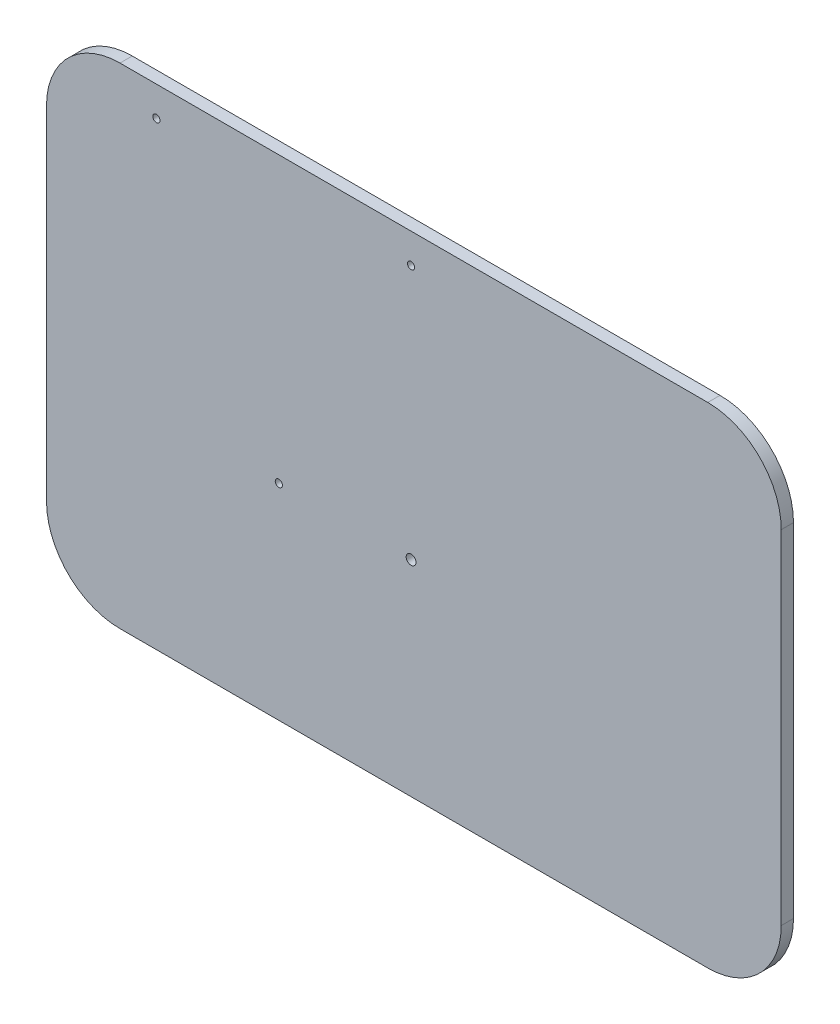
SolidWorks part; units mm, degrees
ref_plane "Alzado" through (0, 0, 0) normal (0, 0, 1) x (1, 0, 0)
ref_plane "Planta" through (0, 0, 0) normal (0, 1, 0) x (1, 0, 0)
ref_plane "Vista lateral" through (0, 0, 0) normal (1, 0, 0) x (0, 0, -1)
sketch "Croquis1" plane through (0, 0, 0) normal (0, 0, 1) x (1, 0, 0)
  line L1 (30, 0) -> (270, 0)
  line L2 (0, 30) -> (0, 170)
  line L3 (30, 200) -> (270, 200)
  line L4 (300, 30) -> (300, 170)
  arc A0 (30, 0) -> (0, 30) centre (30, 30) cw
  arc A1 (270, 0) -> (300, 30) centre (270, 30) ccw
  arc A2 (270, 200) -> (300, 170) centre (270, 170) cw
  arc A3 (0, 170) -> (30, 200) centre (30, 170) cw
  point P7 (0, 0)
  point P12 (300, 200)
  point P15 (0, 200)
  dimension "D3" = 30
  dimension "D1" = 200
  dimension "D2" = 300
extrude "Saliente-Extruir1" add sketch "Croquis1" along normal blind 5
sketch "Croquis2" plane through (0, 0, 0) normal (0, 0, -1) x (-1, 0, 0)
  line L0 (0, 170) -> (0, 30) construction
  line L1 (-270, 200) -> (-30, 200) construction
  circle A0 centre (-148.8517, 187.8414) radius 1.4655
  circle A1 centre (-44.8517, 187.8414) radius 1.4655
  circle A2 centre (-94.8517, 83.8414) radius 1.4655
  circle A3 centre (-148.8517, 83.8414) radius 2
  point P12 (-44.8517, 187.8414)
  dimension "D1" = 4
  dimension "D2" = 44.8517
  dimension "D3" = 12.1586
extrude "Cortar-Extruir1" cut sketch "Croquis2" against normal blind 5
sketch "Croquis3" plane through (0, 0, 0) normal (0, 0, -1) x (-1, 0, 0)
  line L4 (0, 30) -> (0, 170)
  line L5 (-30, 200) -> (-270, 200)
  line L6 (-300, 170) -> (-300, 30)
  line L7 (-270, 0) -> (-30, 0)
  line L8 (0, 30) -> (0, 170)
  line L9 (-30, 200) -> (-270, 200)
  line L10 (-300, 170) -> (-300, 30)
  line L11 (-270, 0) -> (-30, 0)
  circle A0 centre (-148.8517, 83.8414) radius 2 construction
  circle A1 centre (-94.8517, 83.8414) radius 1.4655 construction
  circle A2 centre (-44.8517, 187.8414) radius 1.4655 construction
  circle A3 centre (-148.8517, 187.8414) radius 1.4655 construction
  arc A4 (-30, 0) -> (0, 30) centre (-30, 30) ccw
  arc A5 (0, 170) -> (-30, 200) centre (-30, 170) ccw
  arc A6 (-270, 200) -> (-300, 170) centre (-270, 170) ccw
  arc A7 (-300, 30) -> (-270, 0) centre (-270, 30) ccw
  arc A8 (-30, 0) -> (0, 30) centre (-30, 30) ccw
  arc A9 (0, 170) -> (-30, 200) centre (-30, 170) ccw
  arc A10 (-270, 200) -> (-300, 170) centre (-270, 170) ccw
  arc A11 (-300, 30) -> (-270, 0) centre (-270, 30) ccw
  circle A12 centre (-148.8517, 83.8414) radius 2
  circle A13 centre (-94.8517, 83.8414) radius 1.4655
  circle A14 centre (-44.8517, 187.8414) radius 1.4655
  circle A15 centre (-148.8517, 187.8414) radius 1.4655
  dimension "D1" = 0
